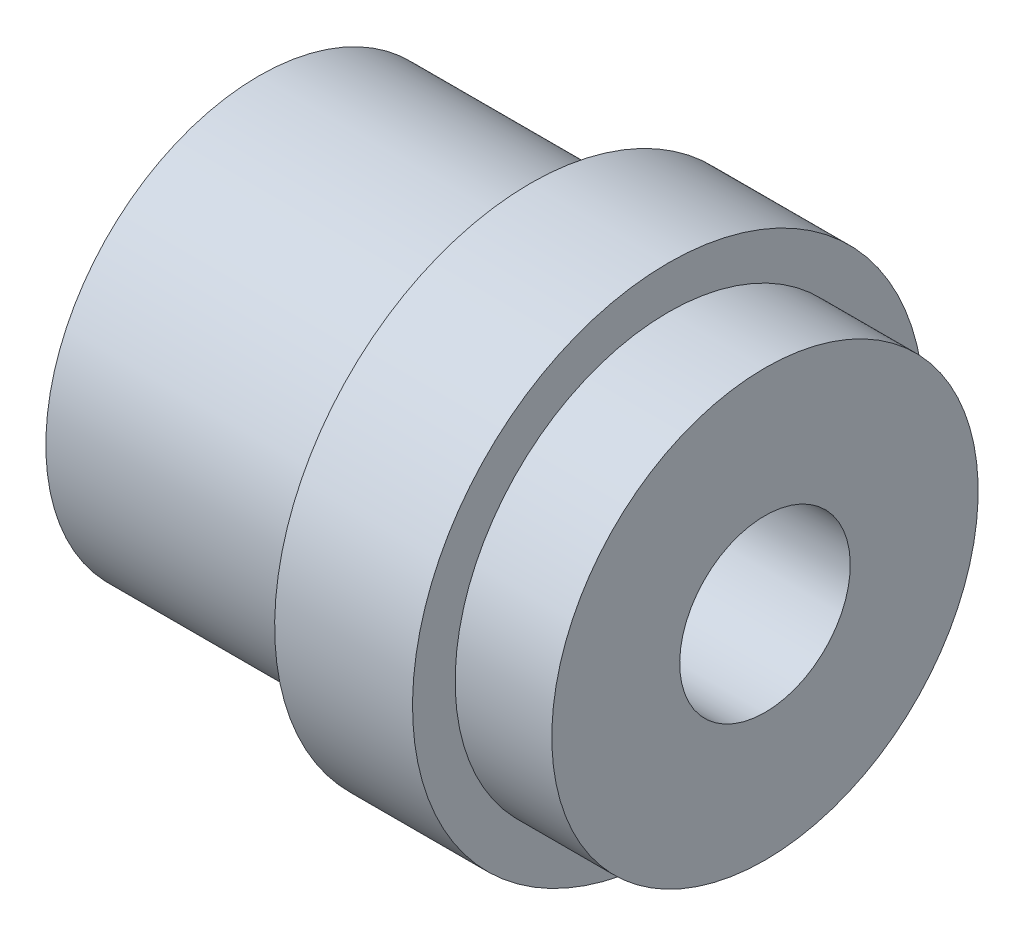
SolidWorks part; units mm, degrees
ref_plane "Front Plane" through (0, 0, 0) normal (0, 0, 1) x (1, 0, 0)
ref_plane "Top Plane" through (0, 0, 0) normal (0, 1, 0) x (1, 0, 0)
ref_plane "Right Plane" through (0, 0, 0) normal (1, 0, 0) x (0, 0, -1)
sketch "Sketch1" plane through (0, 0, 0) normal (0, 0, 1) x (1, 0, 0)
  line L0 (0, 0) -> (-17.8, 0) construction
  line L1 (-17.8, 0) -> (-17.8, 7.5)
  line L2 (-17.8, 7.5) -> (-8.25, 7.5)
  line L3 (-8.25, 7.5) -> (-8.25, 9)
  line L4 (-8.25, 9) -> (-3.4, 9)
  line L5 (-3.4, 9) -> (-3.4, 7.5)
  line L6 (-3.4, 7.5) -> (0, 7.5)
  line L7 (0, 7.5) -> (0, 0)
  line L8 (-17.8, 0) -> (0, 0)
  dimension "D1" = 7.5
  dimension "D2" = 9.55
  dimension "D3" = 1.5
  dimension "D4" = 4.85
  dimension "D5" = 3.4
revolve "Revolve1" add sketch "Sketch1" angle 360 about L0
sketch "Sketch2" plane through (-17.8, 0, 0) normal (-1, 0, 0) x (0, 0, 1)
  circle A0 centre (0, 0) radius 3
  dimension "D1" = 6
extrude "Cut-Extrude1" cut sketch "Sketch2" against normal through all
